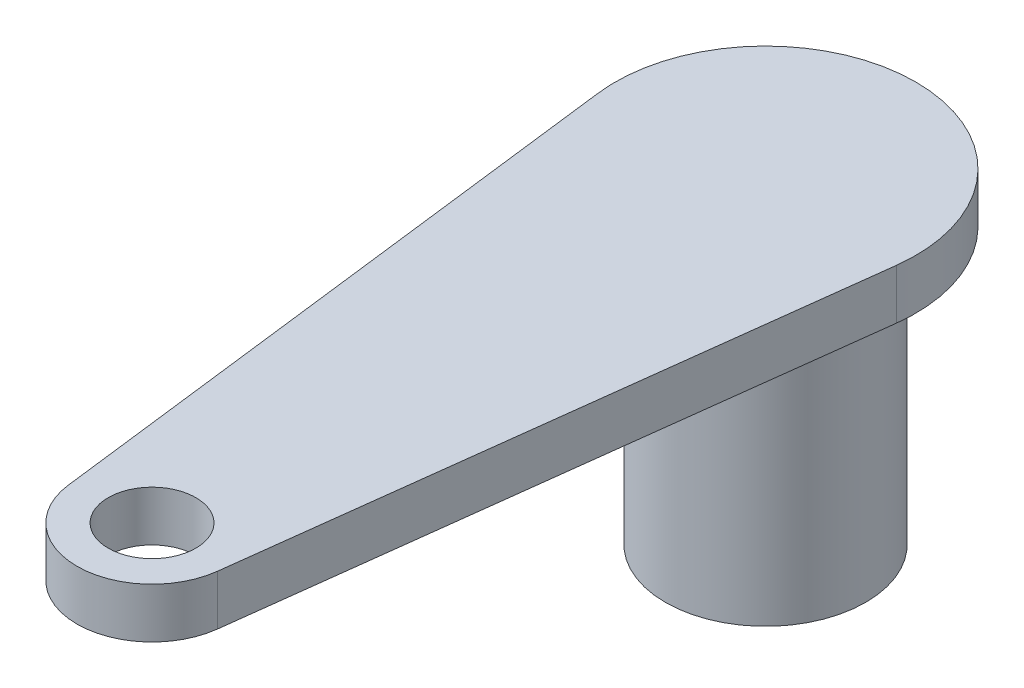
SolidWorks part; units mm, degrees
ref_plane "Front Plane" through (0, 0, 0) normal (0, 0, 1) x (1, 0, 0)
ref_plane "Top Plane" through (0, 0, 0) normal (0, 1, 0) x (1, 0, 0)
ref_plane "Right Plane" through (0, 0, 0) normal (1, 0, 0) x (0, 0, -1)
sketch "Sketch1" plane through (0, 0, 0) normal (0, 1, 0) x (1, 0, 0)
  circle A0 centre (0, 0) radius 3
  circle A1 centre (0, 0) radius 4
  dimension "D1" = 6
  dimension "D2" = 8
extrude "Boss-Extrude1" add sketch "Sketch1" along normal blind 11
sketch "Sketch2" plane through (0, 11, 0) normal (0, 1, 0) x (1, 0, 0)
  line L0 (0, 0) -> (0, -24.5)
  circle A0 centre (0, 0) radius 24.5
  circle A1 centre (0, 0) radius 27.5
  circle A2 centre (0, -24.5) radius 1.75
  dimension "D1" = 49
  dimension "D2" = 55
  dimension "D3" = 3.5
extrude "Boss-Extrude2" add sketch "Sketch2" along normal blind 2 separate body
sketch "Sketch3" plane through (0, 13, 0) normal (0, 1, 0) x (1, 0, 0)
  line L0 (-2.9774, -24.8673) -> (-5.9548, -0.7347)
  line L1 (2.9774, -24.8673) -> (5.9548, -0.7347)
  circle A0 centre (0, 0) radius 4 construction
  circle A1 centre (0, 0) radius 3 construction
  circle A2 centre (0, 0) radius 4
  circle A3 centre (0, 0) radius 3
  circle A4 centre (0, 0) radius 6
  circle A5 centre (0, -24.5) radius 1.75 construction
  circle A6 centre (0, -24.5) radius 1.75
  circle A7 centre (0, -24.5) radius 3
  circle A10 centre (0, 0) radius 27.5 construction
  circle A11 centre (0, 0) radius 41.6852
  circle M9 centre (0, 0) radius 27.5
  dimension "D1" = 12
extrude "Cut-Extrude2" cut sketch "Sketch3" against normal through all contours A7 L0 A4 L1 M9 | A11 M9
